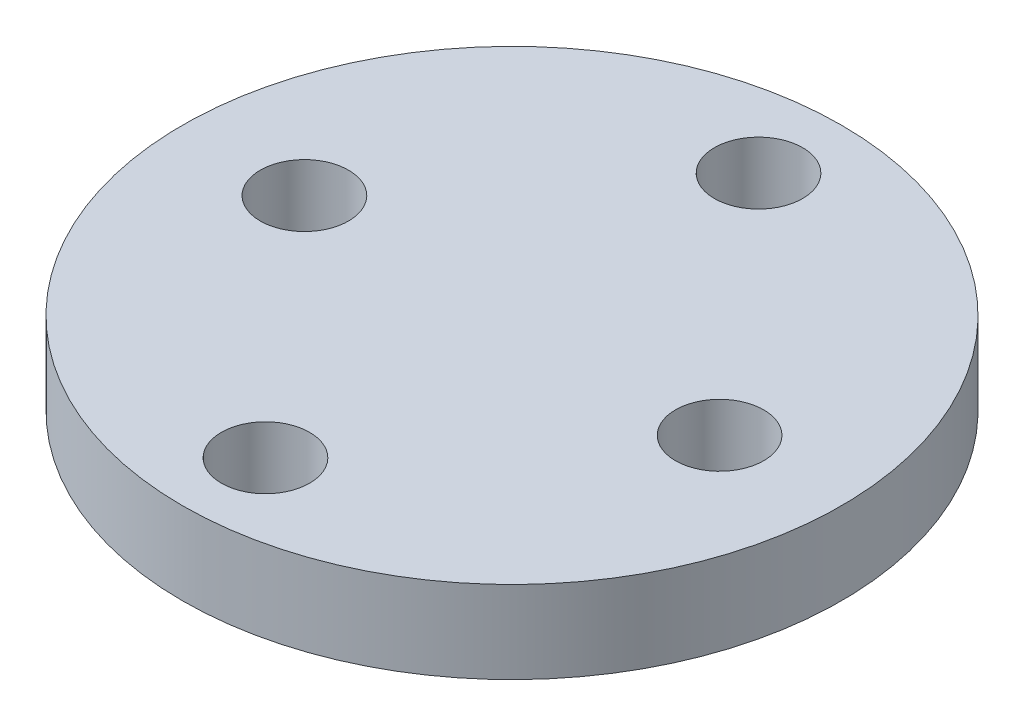
SolidWorks part; units mm, degrees
material "Nylon 101"
ref_plane "Front Plane" through (0, 0, 0) normal (0, 0, 1) x (1, 0, 0)
ref_plane "Top Plane" through (0, 0, 0) normal (0, 1, 0) x (1, 0, 0)
ref_plane "Right Plane" through (0, 0, 0) normal (1, 0, 0) x (0, 0, -1)
sketch "Sketch1" plane through (0, 0, 0) normal (0, 1, 0) x (1, 0, 0)
  line L0 (0, -12.7) -> (0, 12.7) construction
  line L1 (-12.7, 0) -> (12.7, 0) construction
  circle A0 centre (0, 0) radius 12.7
  circle A1 centre (0, 0) radius 8 construction
  circle A2 centre (0, 0) radius 9.5 construction
  circle A3 centre (0, 9.5) radius 1.7
  circle A4 centre (0, -9.5) radius 1.7
  circle A5 centre (-8, 0) radius 1.7
  circle A6 centre (8, 0) radius 1.7
  point P15 (0, 0)
  point P20 (0, 0)
  dimension "D1" = 25.4
  dimension "D2" = 16
  dimension "D3" = 19
  dimension "D4" = 3.4
  dimension "D6" = 3.4
  dimension "D5" = 2
  dimension "D7" = 2
extrude "Boss-Extrude1" add sketch "Sketch1" along normal blind 3.175
